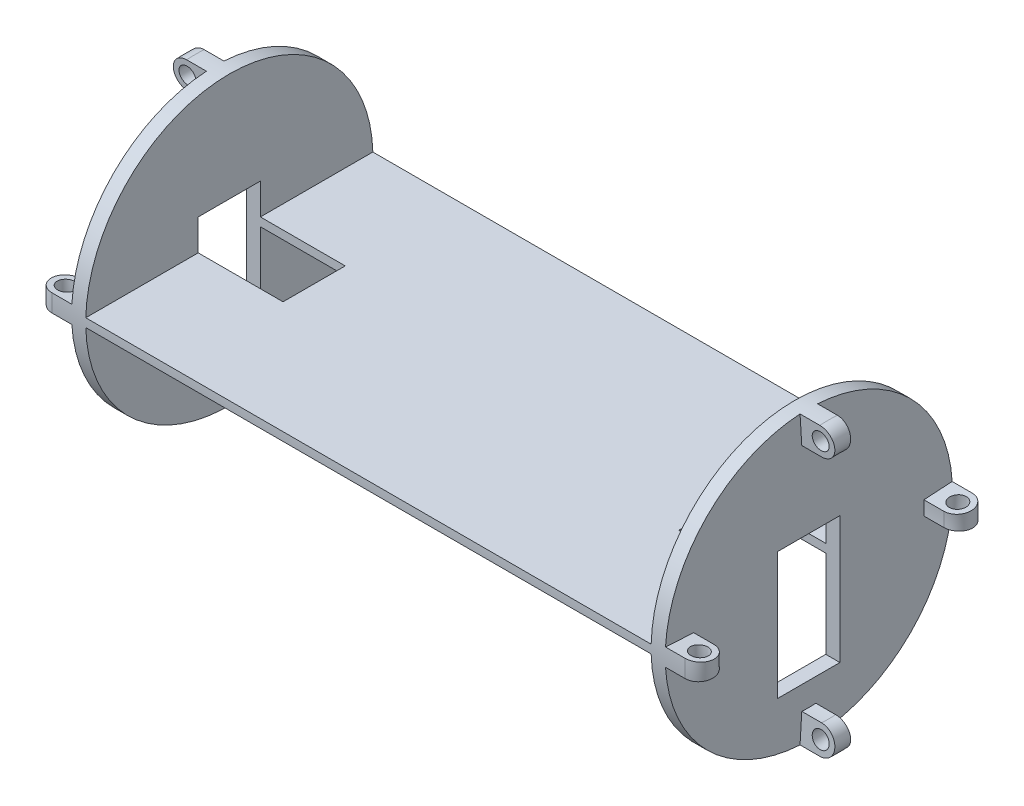
SolidWorks part; units mm, degrees
ref_plane "Front Plane" through (0, 0, 0) normal (0, 0, 1) x (1, 0, 0)
ref_plane "Top Plane" through (0, 0, 0) normal (0, 1, 0) x (1, 0, 0)
ref_plane "Right Plane" through (0, 0, 0) normal (1, 0, 0) x (0, 0, -1)
sketch "Sketch1" plane through (0, 0, 0) normal (1, 0, 0) x (0, 0, -1)
  circle A0 centre (0, 0) radius 50.8
  dimension "D1" = 101.6
extrude "Boss-Extrude1" add sketch "Sketch1" against normal blind 5
sketch "Sketch2" plane through (0, 0, 0) normal (1, 0, 0) x (0, 0, -1)
  line L0 (11, 12.5) -> (11, -32.5)
  line L5 (11, -32.5) -> (-11, -32.5)
  line L6 (-11, -32.5) -> (-11, 12.5)
  line L11 (-11, 12.5) -> (11, 12.5)
  point P2 (0, 12.5)
  dimension "D1" = 22
  dimension "D2" = 45
  dimension "D3" = 12.5
ref_plane "Plane1" through (0, 45.72, 0) normal (0, 1, 0) x (1, 0, 0)
extrude "Cut-Extrude1" cut sketch "Sketch2" against normal up to surface (5 mm away) up to face at (-5, 0, -50.8)
sketch "Sketch3" plane through (0, 0, 0) normal (0, 0, 1) x (1, 0, 0)
  line L0 (0, -50.8) -> (0, 50.8) construction
  line L1 (0, -50.8) -> (0, 50.8)
  line L2 (0, 50.8) -> (7, 50.8)
  line L3 (7, 40.8) -> (0, 40.8)
  line L4 (0, 40.8) -> (0, 50.8)
  line L5 (0, 0) -> (45.3261, 0) construction
  arc A0 (7, 50.8) -> (7, 40.8) centre (7, 45.8) cw
  circle A1 centre (7, 45.8) radius 3
  dimension "D2" = 2
  dimension "D1" = 10
  dimension "D3" = 7
revolve "Revolve1" add sketch "Sketch3" angle 7 mid plane about L5
pattern_circular "CirPattern1" count 4 over 360 about axis through (-5, 0, 0) along (1, 0, 0) of "Revolve1"
sketch "Sketch4" plane through (-5, 0, 0) normal (-1, 0, 0) x (0, 0, 1)
  line L0 (-50.7778, 1.5) -> (50.7778, 1.5)
  line L1 (-50.7778, -1.5) -> (50.7778, -1.5)
  circle A0 centre (0, 0) radius 50.8 construction
  arc A1 (-50.7778, 1.5) -> (-50.7778, -1.5) centre (0, 0) ccw
  arc A2 (50.7778, -1.5) -> (50.7778, 1.5) centre (0, 0) ccw
  point P10 (50.8, 0)
  line M3 (-11, -32.5) -> (-11, 12.5)
  line M5 (11, 12.5) -> (11, -32.5)
  circle M7 centre (0, 0) radius 50.8
  dimension "D1" = 3
extrude "Boss-Extrude2" add sketch "Sketch4" along normal blind 200 contours L1 L0 M5 M7 | L1 L0 M3 M5 | L1 L0 M7 M3
sketch "Sketch5" plane through (0, -1.5, 0) normal (0, -1, 0) x (1, 0, 0)
  line L0 (-5, -11) -> (-5, 11) construction
  line L1 (-5, -11) -> (-5, 11)
  line L2 (-5, 11) -> (-35, 11)
  line L3 (-35, 11) -> (-35, -11)
  line L4 (-35, -11) -> (-5, -11)
  line L6 (-5, -50.7778) -> (-5, -11)
  line L7 (-5, -11) -> (-5, 11)
  line L8 (-5, 11) -> (-5, 50.7778)
  line L9 (-5, 50.7778) -> (-205, 50.7778)
  line L10 (-205, 50.7778) -> (-205, -50.7778)
  line L11 (-205, -50.7778) -> (-5, -50.7778)
  line L12 (-5, -50.7778) -> (-5, -11) construction
  line L13 (-5, -11) -> (-5, 11)
  line L14 (-5, 11) -> (-5, 50.7778) construction
  line L15 (-5, 50.7778) -> (-205, 50.7778)
  line L16 (-205, 50.7778) -> (-205, -50.7778)
  line L17 (-205, -50.7778) -> (-5, -50.7778)
  line M9 (-5, -11) -> (-5, 11)
  dimension "D2" = 30
  dimension "D1" = 0
extrude "Cut-Extrude2" cut sketch "Sketch5" against normal up to surface (3 mm away) contours L3 L4 L2 M9 up to face at (-71.6667, 1.5, 0)
ref_plane "Plane2" through (-105, 0, 0) normal (-1, 0, 0) x (0, 0, 1)
mirror "Mirror1" about plane through (-105, 0, 0) normal (-1, 0, 0) of "CirPattern1", "Revolve1", "Cut-Extrude1", "Boss-Extrude1", "Cut-Extrude2"
